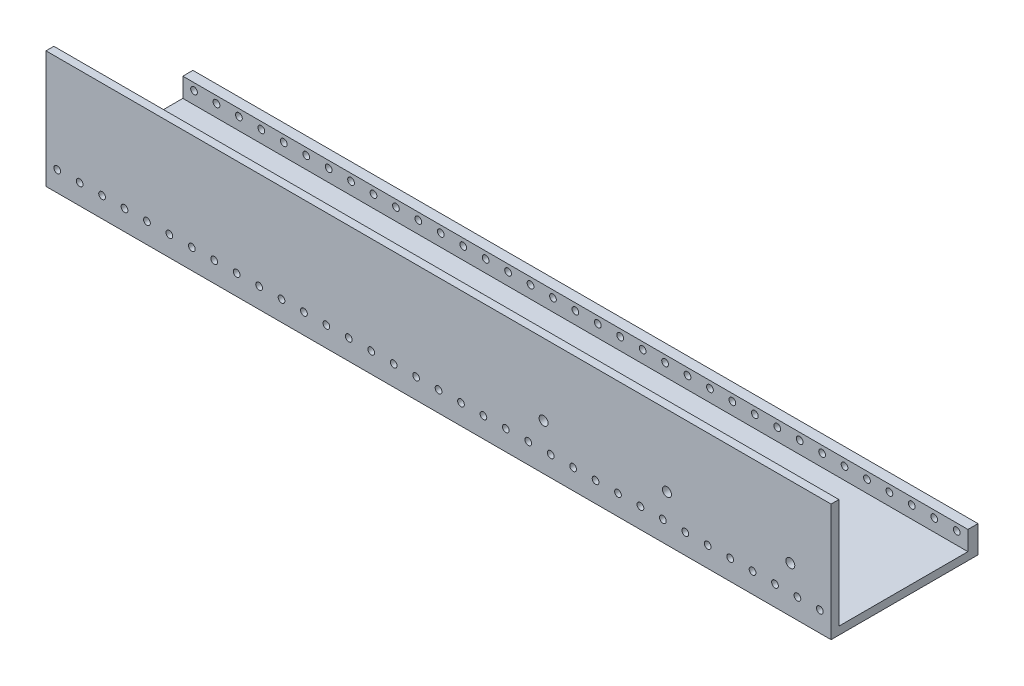
SolidWorks part; units mm, degrees
ref_plane "Front Plane" through (0, 0, 0) normal (0, 0, 1) x (1, 0, 0)
ref_plane "Top Plane" through (0, 0, 0) normal (0, 1, 0) x (1, 0, 0)
ref_plane "Right Plane" through (0, 0, 0) normal (1, 0, 0) x (0, 0, -1)
sketch "Sketch1" plane through (0, 0, 0) normal (0, 0, 1) x (1, 0, 0)
  line L1 (-1750, 350) -> (1750, 350)
  line L2 (-1750, 350) -> (-1750, -350)
  line L3 (-1750, -350) -> (1750, -350)
  line L4 (1750, 350) -> (1750, -350)
  line L5 (0, -350) -> (0, 350) construction
  line L6 (-1750, 0) -> (1750, 0) construction
  point P0 (0, 0)
  dimension "D1" = 3500
  dimension "D2" = 700
extrude "Boss-Extrude1" add sketch "Sketch1" along normal blind 35
sketch "Sketch2" plane through (0, 0, 35) normal (0, 0, 1) x (1, 0, 0)
  line L0 (-2117.4718, 0) -> (2061.5527, 0) construction
  line L1 (0, 922.666) -> (0, -1217.1735) construction
  line L2 (-1750, 350) -> (-1750, -350) construction
  line L3 (-1750, -350) -> (1750, -350) construction
  line L4 (1750, -350) -> (1750, 350) construction
  line L5 (-1750, -350) -> (1750, -350) construction
  circle A0 centre (-1700, -295) radius 15
  circle A1 centre (-1600, -295) radius 15
  circle A2 centre (-1500, -295) radius 15
  circle A6 centre (-1400, -295) radius 15
  circle A7 centre (-1300, -295) radius 15
  circle A8 centre (-1200, -295) radius 15
  circle A9 centre (-1100, -295) radius 15
  circle A10 centre (-1000, -295) radius 15
  circle A11 centre (-900, -295) radius 15
  circle A12 centre (-800, -295) radius 15
  circle A13 centre (-700, -295) radius 15
  circle A14 centre (-600, -295) radius 15
  circle A15 centre (-500, -295) radius 15
  circle A16 centre (-400, -295) radius 15
  circle A17 centre (-300, -295) radius 15
  circle A18 centre (-200, -295) radius 15
  circle A19 centre (-100, -295) radius 15
  circle A20 centre (100, -295) radius 15
  circle A21 centre (200, -295) radius 15
  circle A22 centre (300, -295) radius 15
  circle A23 centre (400, -295) radius 15
  circle A24 centre (500, -295) radius 15
  circle A25 centre (600, -295) radius 15
  circle A26 centre (700, -295) radius 15
  circle A27 centre (800, -295) radius 15
  circle A28 centre (900, -295) radius 15
  circle A29 centre (1000, -295) radius 15
  circle A30 centre (1100, -295) radius 15
  circle A31 centre (1200, -295) radius 15
  circle A32 centre (1300, -295) radius 15
  circle A33 centre (1400, -295) radius 15
  circle A34 centre (1500, -295) radius 15
  circle A35 centre (1600, -295) radius 15
  circle A36 centre (1700, -295) radius 15
  circle A37 centre (0, -295) radius 15
  dimension "D1" = 50
  dimension "D2" = 150
  dimension "D3" = 30
  dimension "D4" = 250
  dimension "D5" = 30
  dimension "D8" = 55
  dimension "D9" = 350
  dimension "D10" = 450
  dimension "D11" = 550
  dimension "D12" = 650
  dimension "D13" = 750
  dimension "D14" = 850
  dimension "D15" = 950
  dimension "D16" = 1050
  dimension "D17" = 1150
  dimension "D18" = 1250
  dimension "D19" = 1350
  dimension "D20" = 1450
  dimension "D21" = 1550
  dimension "D22" = 1650
  dimension "D24" = 1750
  dimension "D6" = 55
  dimension "D7" = 55
  dimension "D23" = 50
  dimension "D25" = 55
  dimension "D26" = 55
  dimension "D27" = 55
  dimension "D28" = 55
  dimension "D29" = 55
  dimension "D30" = 55
  dimension "D31" = 55
  dimension "D32" = 55
  dimension "D33" = 55
  dimension "D34" = 55
  dimension "D35" = 55
  dimension "D36" = 55
  dimension "D37" = 55
  dimension "D38" = 55
  dimension "D39" = 55
extrude "Cut-Extrude1" cut sketch "Sketch2" against normal through all
sketch "Sketch3" plane through (-1750, 0, 0) normal (-1, 0, 0) x (0, 0, 1)
  line L0 (0, -350) -> (610, -350)
  line L1 (610, -350) -> (610, 350)
  dimension "D1" = 610
  dimension "D2" = 700
extrude "Extrude-Thin1" add sketch "Sketch3" against normal blind 3500 thin
sketch "Sketch4" plane through (0, 0, 645) normal (0, 0, 1) x (1, 0, 0)
  circle A0 centre (-1700, -295) radius 15
  circle A1 centre (-1600, -295) radius 15
  circle A2 centre (-1500, -295) radius 15
  circle A3 centre (-1400, -295) radius 15
  circle A4 centre (-1300, -295) radius 15
  circle A5 centre (-1200, -295) radius 15
  circle A6 centre (-1100, -295) radius 15
  circle A7 centre (-1000, -295) radius 15
  circle A8 centre (-900, -295) radius 15
  circle A9 centre (-800, -295) radius 15
  circle A10 centre (-700, -295) radius 15
  circle A11 centre (-600, -295) radius 15
  circle A12 centre (-500, -295) radius 15
  circle A13 centre (-400, -295) radius 15
  circle A14 centre (-300, -295) radius 15
  circle A15 centre (-200, -295) radius 15
  circle A16 centre (-100, -295) radius 15
  circle A17 centre (0, -295) radius 15
  circle A18 centre (100, -295) radius 15
  circle A19 centre (200, -295) radius 15
  circle A20 centre (300, -295) radius 15
  circle A21 centre (400, -295) radius 15
  circle A22 centre (500, -295) radius 15
  circle A23 centre (600, -295) radius 15
  circle A24 centre (700, -295) radius 15
  circle A25 centre (800, -295) radius 15
  circle A26 centre (900, -295) radius 15
  circle A27 centre (1000, -295) radius 15
  circle A28 centre (1100, -295) radius 15
  circle A29 centre (1200, -295) radius 15
  circle A30 centre (1300, -295) radius 15
  circle A31 centre (1400, -295) radius 15
  circle A32 centre (1500, -295) radius 15
  circle A33 centre (1600, -295) radius 15
  circle A34 centre (1700, -295) radius 15
extrude "Cut-Extrude2" cut sketch "Sketch4" against normal through all
sketch "Sketch6" plane through (0, 0, 0) normal (0, 0, -1) x (-1, 0, 0)
  line L0 (1750, 350) -> (1750, -385) construction
  line L1 (-1750, 245.1359) -> (1750, 245.1359)
  line L2 (-1750, 245.1359) -> (-1750, -245.1359)
  line L3 (-1750, -245.1359) -> (1750, -245.1359)
  line L4 (1750, 245.1359) -> (1750, -245.1359)
  line L5 (0, -245.1359) -> (0, 245.1359) construction
  line L6 (-1750, 0) -> (1750, 0) construction
  line L7 (-1750, 350) -> (1750, 350) construction
  line L8 (-1750, 245.1359) -> (-1750, 350)
  line L9 (-1750, 350) -> (1750, 350)
  line L10 (1750, 350) -> (1750, 245.1359)
  line L11 (-1750, 245.1359) -> (1750, 245.1359)
  point P0 (0, 0)
  line M40 (-1750, 350) -> (-1750, -385)
  line M42 (1750, -385) -> (1750, 350)
  line M43 (1750, 350) -> (-1750, 350)
  dimension "D1" = 104.8641
extrude "Cut-Extrude4" cut sketch "Sketch6" against normal blind 80 contours L1 M40 M42 M43 | L3 L1 M40 M42
sketch "Sketch7" plane through (0, 0, 0) normal (0, 0, -1) x (-1, 0, 0)
  line L0 (-1750, -245.1359) -> (-1750, -385)
  line L1 (-1750, -385) -> (1750, -385)
  line L2 (1750, -385) -> (1750, -245.1359)
  line L3 (1750, -245.1359) -> (-1750, -245.1359)
extrude "Boss-Extrude2" add sketch "Sketch7" along normal blind 10
sketch "Sketch8" plane through (0, 0, 610) normal (0, 0, -1) x (-1, 0, 0)
  line L0 (-1750, -385) -> (1750, -385) construction
  line L5 (531.7139, -29.75) -> (531.7139, 62)
  line L6 (531.7139, 62) -> (431.7139, 62)
  line L7 (431.7139, 62) -> (431.7139, -32)
  line L9 (531.7139, -29.75) -> (531.7139, -232)
  line L10 (531.7139, -232) -> (431.7139, -232)
  line L11 (431.7139, -32) -> (431.7139, -232)
  line L12 (481.7139, -232) -> (481.7139, -200) construction
  line L13 (131.7139, 350) -> (131.7139, -245.1359) construction
  line L14 (-1750, 350) -> (1750, 350) construction
  line L15 (1750, -245.1359) -> (-1750, -245.1359) construction
  line L16 (-168.2861, -141.5438) -> (-268.2861, -141.5438)
  line L17 (-168.2861, -141.5438) -> (-168.2861, -232)
  line L18 (-268.2861, -232) -> (-168.2861, -232)
  line L19 (-268.2861, -141.5438) -> (-268.2861, -232)
  line L23 (-493.2861, 350) -> (-493.2861, -245.1359) construction
  line L24 (-718.2861, -232) -> (-818.2861, -232)
  line L25 (-718.2861, -141.5438) -> (-718.2861, -232)
  line L26 (-818.2861, -141.5438) -> (-818.2861, -232)
  line L27 (-818.2861, -141.5438) -> (-718.2861, -141.5438)
  line L28 (-1043.2861, 350) -> (-1043.2861, -232) construction
  line L29 (-1368.2861, -141.5438) -> (-1368.2861, -232)
  line L30 (-1368.2861, -232) -> (-1268.2861, -232)
  line L31 (-1268.2861, -141.5438) -> (-1268.2861, -232)
  line L32 (-1268.2861, -141.5438) -> (-1368.2861, -141.5438)
  circle A0 centre (481.7139, -185) radius 15
  circle A1 centre (481.7139, 15) radius 15
  circle A2 centre (481.7139, -85.9974) radius 15
  circle A5 centre (-218.2861, -185) radius 15
  circle A6 centre (-768.2861, -185) radius 15
  circle A7 centre (-1318.2861, -185) radius 15
  point P42 (844.5024, -93.3897)
  point P43 (844.5024, 16.125)
  point P44 (0, 0)
  point P45 (0, 0)
  point P46 (0, 0)
  point P47 (650.3977, 16.125)
  point P48 (650.3977, -82.7147)
  point P49 (481.7139, -85.9974)
  point P50 (481.7139, 16.125)
  dimension "D1" = 200
  dimension "D6" = 400
  dimension "D2" = 100
  dimension "D3" = 400
  dimension "D7" = 325
  dimension "D8" = 325
extrude "Boss-Extrude3" add sketch "Sketch8" along normal blind 15
sketch "Sketch10" plane through (0, 0, 610) normal (0, 0, -1) x (-1, 0, 0)
  circle A0 centre (481.7139, 15) radius 15
  circle A1 centre (481.7139, -185) radius 15
  circle A3 centre (481.7139, -85.9974) radius 15
extrude "Boss-Extrude4" add sketch "Sketch10" along normal blind 20
sketch "Sketch14" plane through (0, 0, 610) normal (0, 0, -1) x (-1, 0, 0)
  circle A0 centre (-768.2861, -185) radius 15
  circle A1 centre (-1318.2861, -185) radius 15
  circle A2 centre (-218.2861, -185) radius 15
extrude "Boss-Extrude6" add sketch "Sketch14" along normal blind 20
sketch "Sketch15" plane through (-1750, 0, 0) normal (-1, 0, 0) x (0, 0, 1)
  line L0 (35, -245.1359) -> (35, -350) construction
  line L1 (-10.2727, -241.7752) -> (35, -241.7752)
  line L2 (-10.2727, -241.7752) -> (-10.2727, -264.1519)
  line L3 (-10.2727, -264.1519) -> (35, -264.1519)
  line L4 (35, -241.7752) -> (35, -264.1519)
  line L5 (12.3637, -264.1519) -> (12.3637, -241.7752) construction
  line L6 (-10.2727, -252.9635) -> (35, -252.9635) construction
  point P0 (12.3637, -252.9635)
extrude "Cut-Extrude5" cut sketch "Sketch15" against normal through all
sketch "Sketch16" plane through (0, 0, 610) normal (0, 0, -1) x (-1, 0, 0)
  line L0 (-268.2861, -141.5438) -> (-268.2861, -232) construction
  line L1 (-1750, -350) -> (1750, -350) construction
  circle A0 centre (-468.2861, -180) radius 20
  dimension "D1" = 200
  dimension "D2" = 40
  dimension "D3" = 170
extrude "Cut-Extrude6" cut sketch "Sketch16" against normal through all
sketch "Sketch17" plane through (0, 0, 610) normal (0, 0, -1) x (-1, 0, 0)
  line L0 (-818.2861, -141.5438) -> (-818.2861, -232) construction
  line L1 (-1368.2861, -141.5438) -> (-1368.2861, -232) construction
  line L2 (-1750, -350) -> (1750, -350) construction
  circle A0 centre (-1018.2861, -180) radius 20
  circle A1 centre (-1568.1714, -180) radius 20
  point P8 (-1368.2861, -186.7719)
  dimension "D1" = 40
  dimension "D3" = 200
  dimension "D4" = 40
  dimension "D2" = 200
  dimension "D5" = 170
  dimension "D6" = 170
extrude "Cut-Extrude7" cut sketch "Sketch17" against normal through all
sketch "Sketch18" plane through (0, 0, 610) normal (0, 0, -1) x (-1, 0, 0)
  line L0 (-1750, 350) -> (1750, 350)
  line L1 (1750, 350) -> (1750, 138.7006)
  line L2 (1750, -350) -> (1750, 350) construction
  line L3 (1750, 138.7006) -> (-1750, 138.7006)
  line L4 (-1750, -350) -> (-1750, 350) construction
  line L5 (-1750, 138.7006) -> (-1750, 350)
extrude "Cut-Extrude8" cut sketch "Sketch18" against normal through all
